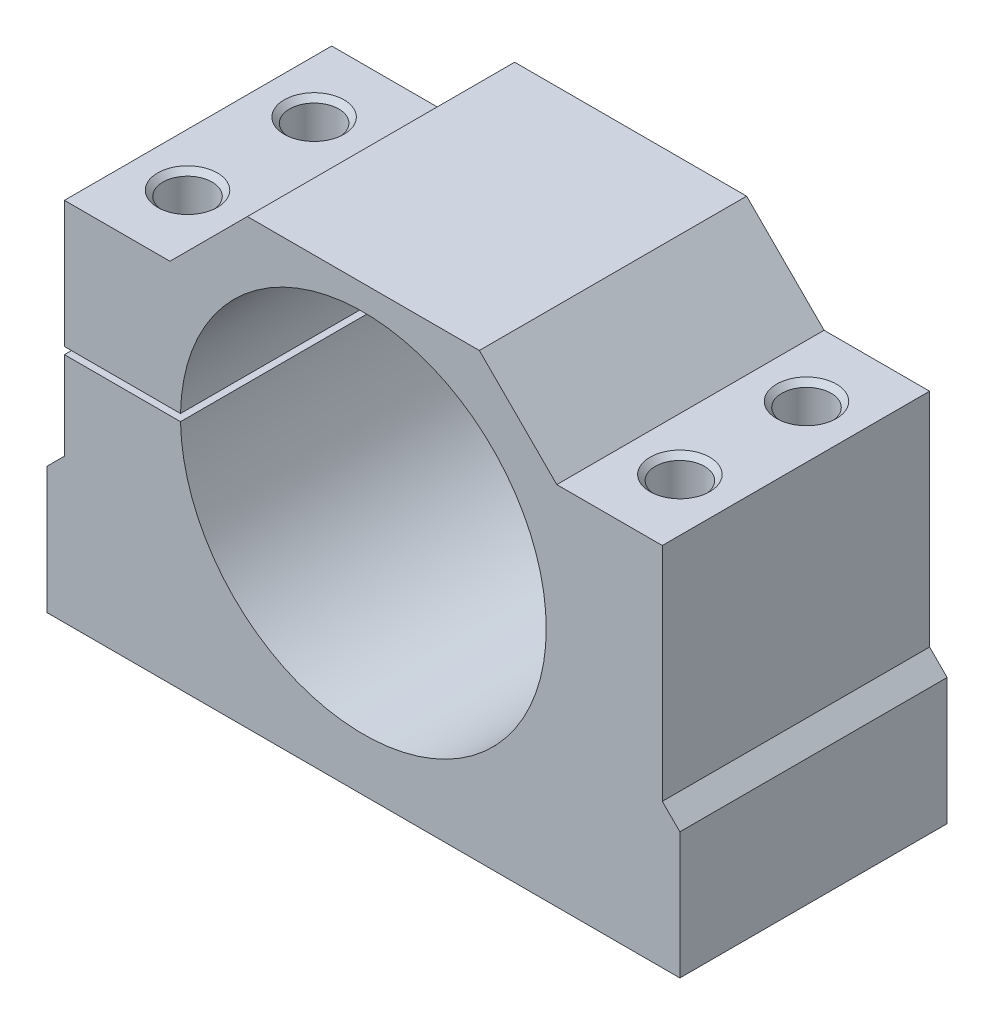
SolidWorks part; units mm, degrees
ref_plane "Ebene vorne" through (0, 0, 0) normal (0, 0, 1) x (1, 0, 0)
ref_plane "Ebene oben" through (0, 0, 0) normal (0, 1, 0) x (1, 0, 0)
ref_plane "Ebene rechts" through (0, 0, 0) normal (1, 0, 0) x (0, 0, -1)
sketch "Skizze1" plane through (0, 0, 0) normal (0, 0, 1) x (1, 0, 0)
  line L0 (0, 0) -> (0, 18)
  line L1 (0, 18) -> (2.5, 20.5)
  line L2 (2.5, 20.5) -> (2.5, 52)
  line L3 (2.5, 52) -> (17.5, 52)
  line L4 (17.5, 52) -> (28.51, 63.01)
  line L5 (28.51, 63.01) -> (61.49, 63.01)
  line L6 (61.49, 63.01) -> (72.5, 52)
  line L7 (72.5, 52) -> (87.5, 52)
  line L8 (87.5, 52) -> (87.5, 20.5)
  line L9 (87.5, 20.5) -> (90, 18)
  line L10 (90, 18) -> (90, 0)
  line L11 (90, 0) -> (0, 0)
  dimension "D1" = 90
  dimension "D2" = 52
  dimension "D3" = 15
  dimension "D4" = 15
  dimension "D5" = 63.01
  dimension "D6" = 18
  dimension "D7" = 18
  dimension "D8" = 52
  dimension "D9" = 2.5
  dimension "D10" = 2.5
  dimension "D11" = 135
  dimension "D12" = 135
  dimension "D13" = 135
extrude "Aufsatz-Linear austragen1" add sketch "Skizze1" along normal blind 38
sketch "Skizze2" plane through (0, 0, 38) normal (0, 0, 1) x (1, 0, 0)
  circle A0 centre (45, 33.5) radius 26
extrude "Schnitt-Linear austragen1" cut sketch "Skizze2" against normal blind 38
sketch "Skizze3" plane through (0, 0, 38) normal (0, 0, 1) x (1, 0, 0)
  line L0 (2.5, 34) -> (19.5, 34)
  line L1 (2.5, 52) -> (2.5, 20.5) construction
  line L2 (19.5, 34) -> (19.5, 33)
  line L3 (19.5, 33) -> (2.5, 33)
  line L4 (2.5, 33) -> (2.5, 34)
  line L5 (0, 0) -> (90, 0) construction
  dimension "D1" = 1
  dimension "D2" = 33
  dimension "D3" = 17
extrude "Schnitt-Linear austragen2" cut sketch "Skizze3" against normal blind 38
hole_wizard "Ø7.0 (7) Durchmesser Bohrung4" positions "Skizze11" profile "Skizze10" hole size "Ø7.0" standard "DIN" end condition through all
sketch "Skizze11" plane through (0, 52, 0) normal (0, 1, 0) x (1, 0, 0)
  point P0 (10, -10)
  point P1 (10, -28)
  point P2 (80, -28)
  point P3 (80, -10)
sketch "Skizze10" plane through (10, 52, 10) normal (1, 0, 0) x (0, 0, 1)
  line L0 (0, 0) -> (0, 52)
  line L1 (0, 52) -> (3.5, 52)
  line L2 (3.5, 52) -> (3.5, 0.75)
  line L3 (3.5, 0.75) -> (4.25, 0)
  line L5 (4.25, 0) -> (0, 0)
  line L6 (-3.5, 0.75) -> (-4.25, 0) construction
  line L11 (0, -6.35) -> (0, 107.95) construction
  dimension "Bohrerdurchmesser" = 7
  dimension "Bohrungstiefe" = 52
  dimension "Senkdurchmesser2 (Oben)" = 8.5
  dimension "Senkwinkel2 (Oben)" = 90
